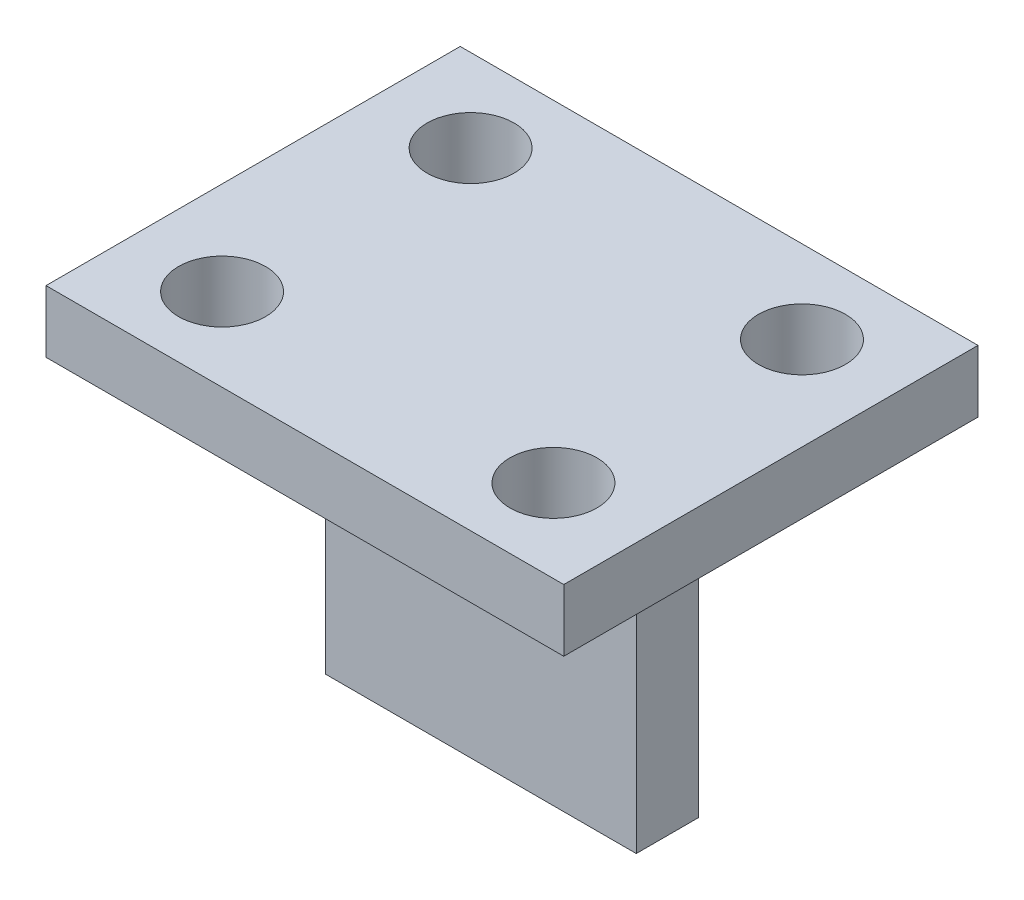
SolidWorks part; units mm, degrees
ref_plane "Front Plane" through (0, 0, 0) normal (0, 0, 1) x (1, 0, 0)
ref_plane "Top Plane" through (0, 0, 0) normal (0, 1, 0) x (1, 0, 0)
ref_plane "Right Plane" through (0, 0, 0) normal (1, 0, 0) x (0, 0, -1)
sketch "Sketch1" plane through (0, 0, 0) normal (0, 1, 0) x (1, 0, 0)
  line L1 (-12.5, -10) -> (12.5, -10)
  line L2 (-12.5, -10) -> (-12.5, 10)
  line L3 (-12.5, 10) -> (12.5, 10)
  line L4 (12.5, -10) -> (12.5, 10)
  line L5 (-12.5, -10) -> (12.5, 10) construction
  line L6 (-12.5, 10) -> (12.5, -10) construction
  point P0 (0, 0)
  dimension "D1" = 25
  dimension "D2" = 20
extrude "Boss-Extrude1" add sketch "Sketch1" along normal mid plane 3
sketch "Sketch2" plane through (0, -1.5, 0) normal (0, -1, 0) x (1, 0, 0)
  line L1 (-7.5, -1.5) -> (7.5, -1.5)
  line L2 (-7.5, -1.5) -> (-7.5, 1.5)
  line L3 (-7.5, 1.5) -> (7.5, 1.5)
  line L4 (7.5, -1.5) -> (7.5, 1.5)
  line L5 (-7.5, -1.5) -> (7.5, 1.5) construction
  line L6 (-7.5, 1.5) -> (7.5, -1.5) construction
  point P0 (0, 0)
  dimension "D1" = 15
  dimension "D2" = 3
extrude "Boss-Extrude2" add sketch "Sketch2" along normal blind 15
sketch "Sketch3" plane through (0, 1.5, 0) normal (0, 1, 0) x (1, 0, 0)
  line L0 (-1.65, 0) -> (1.65, 0) construction
  circle A0 centre (-8, 6) radius 2.1
  circle A1 centre (8, 6) radius 2.1
  circle A2 centre (8, -6) radius 2.1
  circle A3 centre (-8, -6) radius 2.1
  dimension "D3" = 4.2
  dimension "D1" = 8
  dimension "D2" = 6
  dimension "D4" = 2
  dimension "D5" = 2
extrude "Cut-Extrude1" cut sketch "Sketch3" against normal up to next and the other way through all
